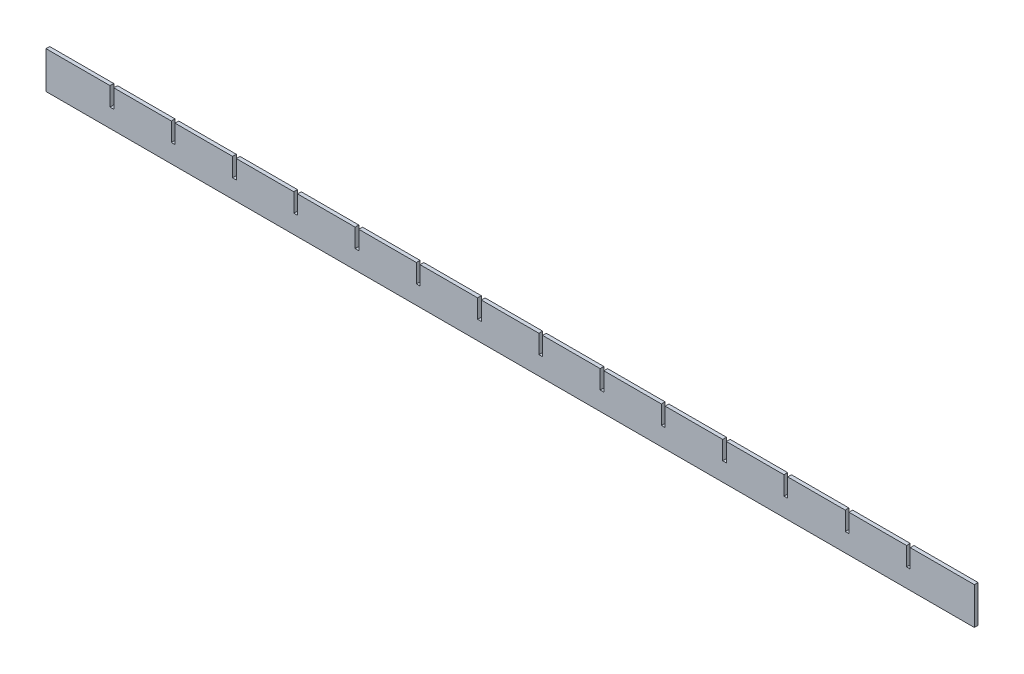
SolidWorks part; units mm, degrees
ref_plane "Plan de face" through (0, 0, 0) normal (0, 0, 1) x (1, 0, 0)
ref_plane "Plan de dessus" through (0, 0, 0) normal (0, 1, 0) x (1, 0, 0)
ref_plane "Plan de droite" through (0, 0, 0) normal (1, 0, 0) x (0, 0, -1)
sketch "Esquisse1" plane through (0, 0, 0) normal (0, 0, 1) x (1, 0, 0)
  line L1 (-250, -10) -> (250, -10)
  line L2 (-250, -10) -> (-250, 10)
  line L3 (-250, 10) -> (250, 10)
  line L4 (250, -10) -> (250, 10)
  line L5 (-250, -10) -> (250, 10) construction
  line L6 (-250, 10) -> (250, -10) construction
  point P0 (0, 0)
  dimension "D1" = 20
  dimension "D2" = 500
extrude "Boss.-Extru.1" add sketch "Esquisse1" along normal mid plane 2
sketch "Esquisse2" plane through (0, 0, 1) normal (0, 0, 1) x (1, 0, 0)
  line L0 (250, 10) -> (-250, 10) construction
  line L1 (15.5, 0) -> (17.5, 0)
  line L2 (15.5, 0) -> (15.5, 10)
  line L3 (15.5, 10) -> (17.5, 10)
  line L4 (17.5, 0) -> (17.5, 10)
  line L5 (16.5, 0) -> (0, 0) construction
  dimension "D1" = 2
  dimension "D2" = 16.5
extrude "Enlèv. mat.-Extru.1" cut sketch "Esquisse2" against normal through all
pattern_linear "Répétition linéaire1" count 7 spacing 33 along (1, 0, 0) of "Enlèv. mat.-Extru.1"
mirror "Symétrie1" about plane through (0, 0, 0) normal (1, 0, 0) of "Répétition linéaire1", "Enlèv. mat.-Extru.1"
